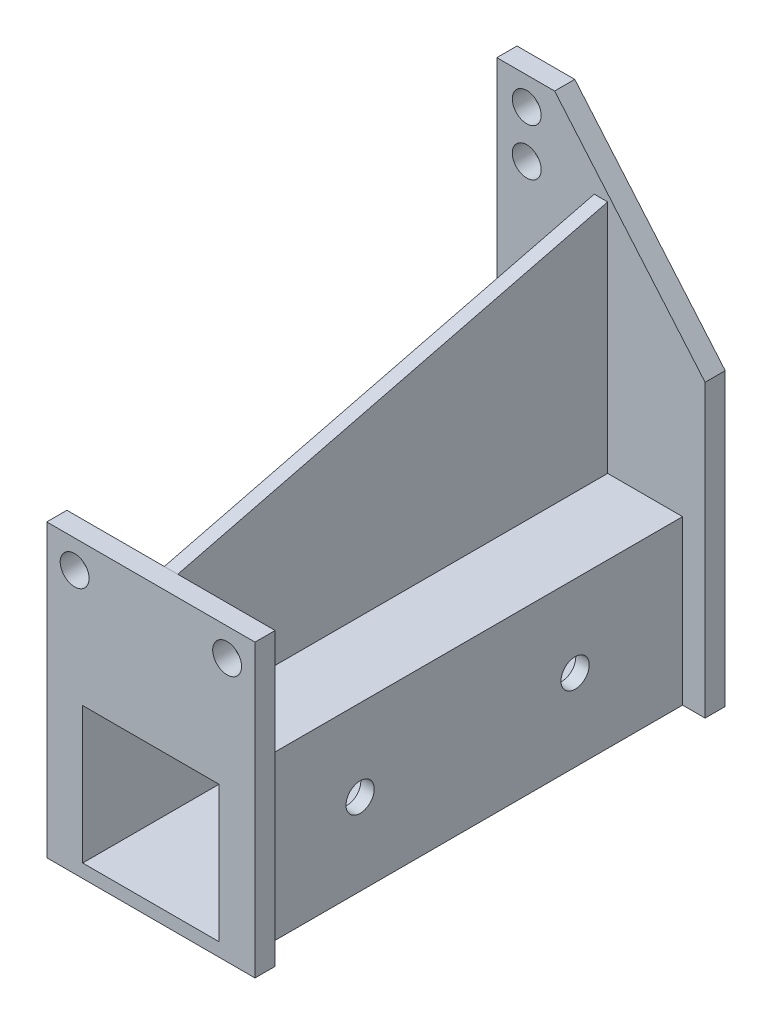
SolidWorks part; units mm, degrees
material "ABS"
ref_plane "Alzado" through (0, 0, 0) normal (0, 0, 1) x (1, 0, 0)
ref_plane "Planta" through (0, 0, 0) normal (0, 1, 0) x (1, 0, 0)
ref_plane "Vista lateral" through (0, 0, 0) normal (1, 0, 0) x (0, 0, -1)
sketch "Croquis1" plane through (0, 0, 0) normal (0, 0, 1) x (1, 0, 0)
  line L1 (-10.15, -10.15) -> (10.15, -10.15)
  line L2 (-10.15, -10.15) -> (-10.15, 10.15)
  line L3 (-10.15, 10.15) -> (10.15, 10.15)
  line L4 (10.15, -10.15) -> (10.15, 10.15)
  line L5 (-10.15, -10.15) -> (10.15, 10.15) construction
  line L6 (-10.15, 10.15) -> (10.15, -10.15) construction
  line L7 (-12.15, -12.15) -> (12.15, -12.15)
  line L8 (-12.15, -12.15) -> (-12.15, 12.15)
  line L9 (-12.15, 12.15) -> (12.15, 12.15)
  line L10 (12.15, -12.15) -> (12.15, 12.15)
  line L11 (-12.15, -12.15) -> (12.15, 12.15) construction
  line L12 (-12.15, 12.15) -> (12.15, -12.15) construction
  point P0 (0, 0)
  point P6 (0, 0)
  dimension "D1" = 20.3
  dimension "D2" = 20.3
  dimension "D3" = 2
extrude "Saliente-Extruir1" add sketch "Croquis1" along normal mid plane 70
sketch "Croquis2" plane through (0, 0, 35) normal (0, 0, 1) x (1, 0, 0)
  line L0 (10.15, 10.15) -> (10.15, 47.2405) construction
  line L1 (10.15, 27) -> (30.7862, 27)
  line L2 (0, 0) -> (0, 51.7804) construction
  line L3 (-15.5, -12.15) -> (-15.5, 31.15)
  line L4 (-15.5, 31.15) -> (15.5, 31.15)
  line L5 (15.5, 31.15) -> (15.5, -12.15)
  line L6 (-12.15, -12.15) -> (-15.5, -12.15)
  line L7 (12.15, -12.15) -> (15.5, -12.15)
  circle A0 centre (11.35, 27) radius 2.15
  circle A1 centre (-11.35, 27) radius 2.15
  dimension "D2" = 4.3
  dimension "D5" = 2
  dimension "D1" = 16.85
  dimension "D3" = 1.2
  dimension "D4" = 2
extrude "Saliente-Extruir2" add sketch "Croquis2" against normal blind 3
sketch "Croquis3" plane through (0, 0, -35) normal (0, 0, -1) x (-1, 0, 0)
  line L0 (0, 0) -> (0, 93.2763) construction
  line L1 (10.15, 10.15) -> (10.15, 93.2763) construction
  line L2 (10.15, 46.35) -> (69.3601, 46.35) construction
  line L3 (10.15, 53.35) -> (84.6724, 53.35) construction
  line L4 (15.5, -12.15) -> (15.5, 57.5)
  line L5 (15.5, 57.5) -> (6.9, 57.5)
  line L6 (6.9, 57.5) -> (-15.5, 31.15)
  line L7 (-15.5, 31.15) -> (-15.5, -12.15)
  line L8 (-15.5, -12.15) -> (-12.15, -12.15)
  line L9 (12.15, -12.15) -> (15.5, -12.15)
  circle A0 centre (11.05, 46.35) radius 2.15
  circle A1 centre (11.05, 53.35) radius 2.15
  line M7 (-12.15, 12.15) -> (-12.15, -12.15)
  line M9 (12.15, -12.15) -> (12.15, 12.15)
  line M10 (12.15, 12.15) -> (-12.15, 12.15)
  dimension "D3" = 4.3
  dimension "D4" = 4.3
  dimension "D6" = 2
  dimension "D7" = 2
  dimension "D1" = 36.2
  dimension "D2" = 43.2
  dimension "D5" = 0.9
extrude "Saliente-Extruir3" add sketch "Croquis3" against normal blind 3 contours L9 L4 L5 L6 L7 L8 A1 A0 M9 M7 M10
sketch "Croquis4" plane through (0, 0, 0) normal (1, 0, 0) x (0, 0, -1)
  line L0 (-32, 12.15) -> (32, 12.15)
  line L1 (-32, 12.15) -> (32, 12.15) construction
  line L2 (-32, 31.15) -> (-32, -12.15) construction
  line L3 (-32, 12.15) -> (-32, 31.15)
  line L4 (-32, 31.15) -> (32, 47.15)
  line L5 (32, 47.15) -> (32, 12.15)
  dimension "D1" = 35
extrude "Saliente-Extruir4" add sketch "Croquis4" along normal mid plane 2
sketch "Croquis5" plane through (12.15, 0, 0) normal (1, 0, 0) x (0, 0, -1)
  line L0 (0, -19.3492) -> (0, 20.8586) construction
  line L6 (-32, 12.15) -> (32, 12.15) construction
  circle A0 centre (-16, 0) radius 2.1
  circle A1 centre (16, 0) radius 2.1
  dimension "D1" = 4.2
  dimension "D2" = 16
  dimension "D3" = 12.15
extrude "Cortar-Extruir1" cut sketch "Croquis5" against normal through all
